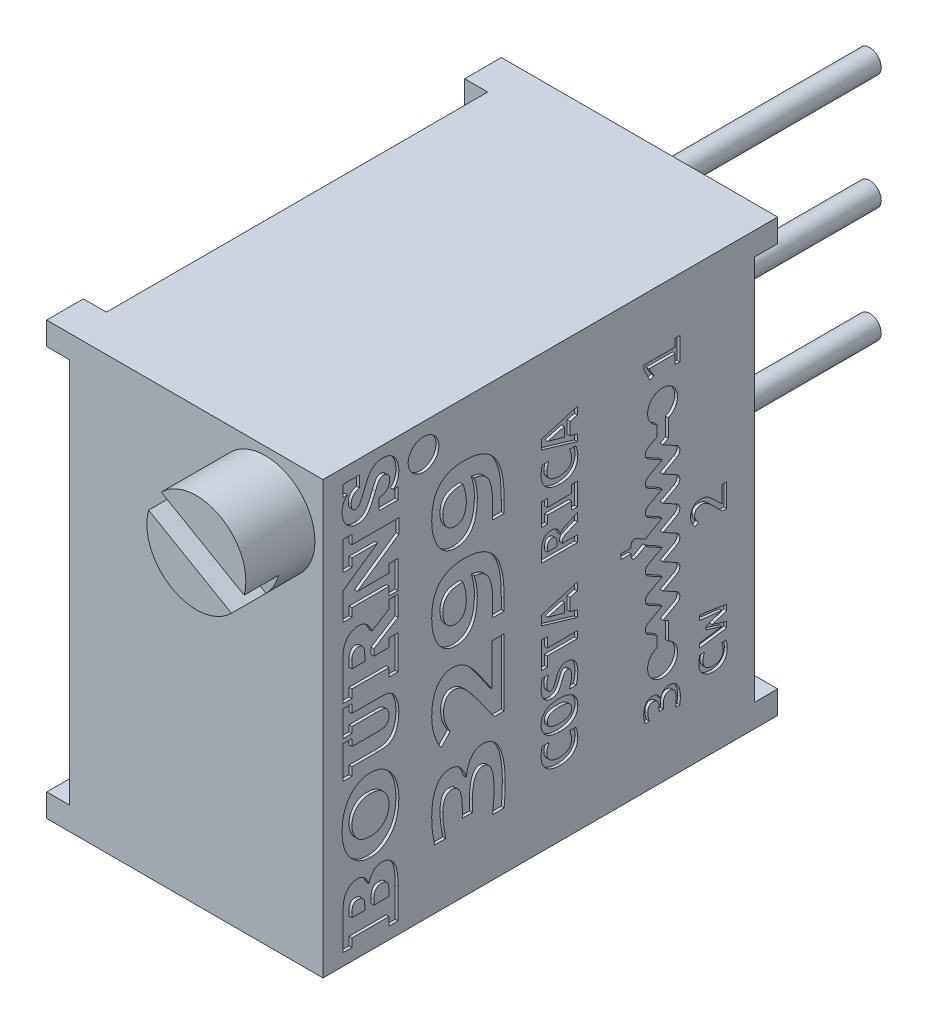
SolidWorks part; units mm, degrees
ref_plane "Front Plane" through (0, 0, 0) normal (0, 0, 1) x (1, 0, 0)
ref_plane "Top Plane" through (0, 0, 0) normal (0, 1, 0) x (1, 0, 0)
ref_plane "Right Plane" through (0, 0, 0) normal (1, 0, 0) x (0, 0, -1)
sketch "Sketch1" plane through (0, 0, 0) normal (0, 0, 1) x (1, 0, 0)
  line L0 (0, 0) -> (0, 2.2225) construction
  line L1 (-1.905, 2.2225) -> (4.191, 2.2225)
  line L2 (-1.905, 2.2225) -> (-1.905, -7.3025)
  line L3 (-1.905, -7.3025) -> (4.191, -7.3025)
  line L4 (4.191, 2.2225) -> (4.191, -7.3025)
  dimension "D1" = 1.905
  dimension "D2" = 6.096
  dimension "D3" = 9.525
  dimension "D4" = 2.2225
extrude "Boss-Extrude1" add sketch "Sketch1" along normal blind 10.033
sketch "Sketch2" plane through (4.191, 0, 0) normal (1, 0, 0) x (0, 0, -1)
  line L0 (0, -7.3025) -> (0, 2.2225) construction
  line L1 (-0.508, 1.7145) -> (0, 1.7145)
  line L2 (-0.508, 1.7145) -> (-0.508, -6.7945)
  line L3 (-0.508, -6.7945) -> (0, -6.7945)
  line L4 (0, 1.7145) -> (0, -6.7945)
  line L5 (-10.033, -7.3025) -> (0, -7.3025) construction
  line L6 (-10.033, 2.2225) -> (0, 2.2225) construction
  dimension "D1" = 0.508
  dimension "D2" = 0.508
  dimension "D3" = 0.508
extrude "Cut-Extrude1" cut sketch "Sketch2" against normal through all
sketch "Sketch3" plane through (0, 0, 0.508) normal (0, 0, -1) x (-1, 0, 0)
  line L0 (-1.143, 2.2225) -> (-1.143, -7.3025) construction
  line L1 (-4.191, 2.2225) -> (1.905, 2.2225) construction
  line L2 (1.905, -7.3025) -> (-4.191, -7.3025) construction
  circle A0 centre (0, 0) radius 0.254
  circle A1 centre (0, -2.54) radius 0.254
  circle A2 centre (0, -5.08) radius 0.254
  dimension "D1" = 0.508
  dimension "D4" = 1.143
  dimension "D3" = 2.54
  dimension "D2" = 3
extrude "Boss-Extrude2" add sketch "Sketch3" along normal blind 6.731
sketch "Sketch4" plane through (-1.905, 0, 0) normal (-1, 0, 0) x (0, 0, 1)
  line L0 (0.508, -6.7945) -> (0.508, 1.7145)
  line L1 (10.033, 2.2225) -> (0, 2.2225) construction
  line L2 (10.033, -7.3025) -> (0, -7.3025) construction
  line L3 (9.2227, 2.2225) -> (9.2227, 1.7145)
  line L4 (0.508, 1.7145) -> (0.508, -6.7945) construction
  line L5 (10.033, 2.2225) -> (10.033, -7.3025) construction
  line L6 (9.2227, 1.7145) -> (10.033, 1.7145)
  line L7 (9.2227, -6.7945) -> (10.033, -6.7945)
  line L8 (0.8103, 2.2225) -> (9.2227, 2.2225)
  line L9 (10.033, 1.7145) -> (10.033, -6.7945)
  line L10 (0.8103, -7.3025) -> (9.2227, -7.3025)
  line L11 (9.2227, -6.7945) -> (9.2227, -7.3025)
  line L12 (0.8103, 2.2225) -> (0.8103, 1.7145)
  line L13 (0.8103, 1.7145) -> (0.508, 1.7145)
  line L14 (0, 2.2225) -> (0, 1.7145) construction
  line L15 (0.8103, -7.3025) -> (0.8103, -6.7945)
  line L16 (0.8103, -6.7945) -> (0.508, -6.7945)
  dimension "D1" = 0.8103
  dimension "D2" = 0.508
  dimension "D3" = 0.508
  dimension "D4" = 0.8103
extrude "Cut-Extrude3" cut sketch "Sketch4" against normal blind 0.508
sketch "Sketch5" plane through (0, 0, 10.033) normal (0, 0, 1) x (1, 0, 0)
  line L0 (4.191, 2.2225) -> (-1.905, 2.2225) construction
  line L1 (4.191, -7.3025) -> (4.191, 2.2225) construction
  circle A0 centre (2.921, 0.9525) radius 1.0922
  dimension "D3" = 2.1844
  dimension "D1" = 1.27
  dimension "D2" = 1.27
extrude "Boss-Extrude3" add sketch "Sketch5" along normal blind 1.524
sketch "Sketch6" plane through (0, 0, 11.557) normal (0, 0, 1) x (1, 0, 0)
  line L0 (1.143, 2.2225) -> (1.143, -0.8608) construction
  line L1 (4.191, 2.2225) -> (-1.905, 2.2225) construction
  line L2 (2.1463, 1.7224) -> (3.9751, 0.6665)
  line L4 (1.8669, 1.2385) -> (3.6957, 0.1826)
  arc A0 (2.1463, 1.7224) -> (1.8669, 1.2385) centre (2.921, 0.9525) ccw
  arc A1 (3.6957, 0.1826) -> (3.9751, 0.6665) centre (2.921, 0.9525) ccw
  dimension "D3" = 1.0922
  dimension "D1" = 0.2794
  dimension "D2" = 0.5588
  dimension "D4" = 60
extrude "Cut-Extrude4" cut sketch "Sketch6" against normal blind 0.762
sketch "Sketch8" plane through (4.191, 0, 0) normal (1, 0, 0) x (0, 0, -1)
  line L0 (-2.54, -4.9784) -> (-2.54, -0.1016) construction
  line L1 (-2.54, -2.54) -> (-0.508, -2.54) construction
  line L2 (-0.508, 1.7145) -> (-0.508, -6.7945) construction
  line L3 (-2.921, -4.2164) -> (-2.159, -4.2164) construction
  line L4 (-2.921, -3.6576) -> (-2.159, -3.6576) construction
  line L5 (-2.921, -3.0988) -> (-2.159, -3.0988) construction
  line L6 (-2.54, -2.54) -> (-2.921, -2.54) construction
  line L7 (-2.921, -1.9812) -> (-2.159, -1.9812) construction
  line L8 (-2.921, -1.4224) -> (-2.159, -1.4224) construction
  line L9 (-2.921, -0.8636) -> (-2.159, -0.8636) construction
  line L10 (-2.54, -4.9784) -> (-2.921, -4.9784) construction
  line L11 (-2.54, -0.1016) -> (-2.921, -0.1016) construction
  line L12 (-2.921, -4.9784) -> (-2.921, -4.2164) construction
  line L13 (-2.921, -4.2164) -> (-2.921, -3.6576) construction
  line L14 (-2.921, -3.6576) -> (-2.921, -3.0988) construction
  line L15 (-2.921, -3.0988) -> (-2.921, -2.54) construction
  line L16 (-2.921, -2.54) -> (-2.921, -1.9812) construction
  line L17 (-2.921, -1.9812) -> (-2.921, -1.4224) construction
  line L18 (-2.921, -1.4224) -> (-2.921, -0.8636) construction
  line L19 (-2.921, -0.8636) -> (-2.921, -0.1016) construction
  line L20 (-2.667, -4.6736) -> (-2.667, -4.4312)
  line L21 (-2.667, -4.4312) -> (-2.8552, -4.3277)
  line L22 (-2.159, -4.2164) -> (-2.159, -0.8636) construction
  line L23 (-2.8552, -4.1051) -> (-2.5495, -3.937)
  line L24 (-2.413, -4.6736) -> (-2.413, -4.281)
  line L25 (-2.413, -4.281) -> (-2.5305, -4.2164)
  line L26 (-2.5305, -4.2164) -> (-2.2248, -4.0483)
  line L27 (-2.667, -4.6736) -> (-2.54, -4.6736) construction
  line L28 (-2.54, -4.6736) -> (-2.413, -4.6736) construction
  line L29 (-2.5495, -3.937) -> (-2.8552, -3.7689)
  line L30 (-2.8552, -3.5463) -> (-2.5495, -3.3782)
  line L31 (-2.5305, -3.6576) -> (-2.2248, -3.8257)
  line L32 (-2.921, -3.937) -> (-2.159, -3.937) construction
  line L33 (-2.5305, -3.6576) -> (-2.2248, -3.4895)
  line L34 (-2.7611, -4.3794) -> (-2.6387, -4.1569) construction
  line L35 (-2.667, -4.4312) -> (-2.413, -4.4312) construction
  line L36 (-2.921, -3.3782) -> (-2.159, -3.3782) construction
  line L37 (-2.921, -2.8194) -> (-2.159, -2.8194) construction
  line L38 (-2.5495, -3.3782) -> (-2.8552, -3.2101)
  line L39 (-2.8552, -2.9875) -> (-2.5495, -2.8194)
  line L40 (-2.921, -2.2606) -> (-2.159, -2.2606) construction
  line L41 (-2.921, -1.7018) -> (-2.159, -1.7018) construction
  line L42 (-2.921, -1.143) -> (-2.159, -1.143) construction
  line L43 (-2.5495, -2.8194) -> (-2.8552, -2.6513)
  line L44 (-2.8552, -2.4287) -> (-2.5495, -2.2606)
  line L45 (-2.5495, -2.2606) -> (-2.8552, -2.0925)
  line L46 (-2.8552, -1.8699) -> (-2.5495, -1.7018)
  line L47 (-2.5495, -1.7018) -> (-2.8552, -1.5337)
  line L48 (-2.8552, -1.3111) -> (-2.5495, -1.143)
  line L49 (-2.5495, -1.143) -> (-2.8552, -0.9749)
  line L50 (-2.8552, -0.7523) -> (-2.667, -0.6488)
  line L51 (-2.667, -0.6488) -> (-2.667, -0.4064)
  line L52 (-2.2248, -3.2669) -> (-2.5305, -3.0988)
  line L53 (-2.5305, -3.0988) -> (-2.2248, -2.9307)
  line L54 (-2.2248, -2.7081) -> (-2.5305, -2.54)
  line L55 (-2.5305, -2.54) -> (-2.2248, -2.3719)
  line L56 (-2.2248, -2.1493) -> (-2.5305, -1.9812)
  line L57 (-2.5305, -1.9812) -> (-2.2248, -1.8131)
  line L58 (-2.2248, -1.5905) -> (-2.5305, -1.4224)
  line L59 (-2.5305, -1.4224) -> (-2.2248, -1.2543)
  line L60 (-2.2248, -1.0317) -> (-2.5305, -0.8636)
  line L61 (-2.5305, -0.8636) -> (-2.413, -0.799)
  line L62 (-2.413, -0.799) -> (-2.413, -0.4064)
  line L63 (-8.3765, -7.3025) -> (-8.3765, 2.2225) construction
  line L64 (-10.033, -7.3025) -> (0, -7.3025) construction
  line L65 (-6.0359, -7.3025) -> (-6.0359, 2.2225) construction
  line L66 (-10.033, 2.2225) -> (0, 2.2225) construction
  line L67 (-2.159, -6.431) -> (-2.159, -5.1421) construction
  line L68 (-2.921, -2.54) -> (-4.274, -2.54) construction
  line L69 (-2.8552, -2.6513) -> (-3.4588, -2.6513) construction
  line L70 (-2.8552, -2.4287) -> (-3.4588, -2.4287) construction
  line L71 (-3.157, -2.6513) -> (-3.157, -2.4287) construction
  line L72 (-3.4588, -2.6513) -> (-3.4588, -2.54) construction
  line L73 (-3.4588, -2.4287) -> (-3.4588, -2.54) construction
  line L74 (-3.4588, -2.5956) -> (-3.2332, -2.5956) construction
  line L75 (-3.4588, -2.4844) -> (-3.2332, -2.4844) construction
  line L76 (-3.1201, -2.362) -> (-2.9189, -2.4733)
  line L77 (-3.1201, -2.718) -> (-2.9189, -2.6067)
  line L78 (-3.2332, -2.6513) -> (-3.2332, -2.5956)
  line L79 (-3.4588, -2.5956) -> (-3.2332, -2.5956)
  line L80 (-3.4588, -2.5956) -> (-3.4588, -2.4844)
  line L81 (-3.4588, -2.4844) -> (-3.2332, -2.4844)
  line L82 (-3.2232, -2.5956) -> (-3.157, -2.5956) construction
  line L83 (-3.2278, -2.4844) -> (-3.157, -2.4844) construction
  line L84 (-3.2332, -2.4844) -> (-3.2332, -2.4287)
  line L85 (-2.159, 0.2344) -> (-2.159, 1.3077) construction
  line L86 (-1.1253, -3.0988) -> (-1.1253, -1.9812) construction
  line L87 (-1.1253, -5.9727) -> (-1.1253, -4.3794) construction
  line L88 (-4.4222, -7.3025) -> (-4.4222, 2.2225) construction
  line L89 (-10.033, -7.3025) -> (-10.033, 2.2225) construction
  arc A0 (-2.667, -4.6736) -> (-2.413, -4.6736) centre (-2.54, -4.9784) ccw
  arc A1 (-2.413, -0.4064) -> (-2.667, -0.4064) centre (-2.54, -0.1016) ccw
  arc A2 (-2.8552, -4.3277) -> (-2.8552, -4.1051) centre (-2.794, -4.2164) cw
  arc A3 (-2.8552, -3.7689) -> (-2.8552, -3.5463) centre (-2.794, -3.6576) cw
  arc A4 (-2.2248, -4.0483) -> (-2.2248, -3.8257) centre (-2.286, -3.937) ccw
  arc A5 (-2.8552, -3.2101) -> (-2.8552, -2.9875) centre (-2.794, -3.0988) cw
  arc A6 (-2.8552, -2.6513) -> (-2.9068, -2.5983) centre (-2.794, -2.54) cw
  arc A7 (-2.8552, -2.0925) -> (-2.8552, -1.8699) centre (-2.794, -1.9812) cw
  arc A8 (-2.8552, -1.5337) -> (-2.8552, -1.3111) centre (-2.794, -1.4224) cw
  arc A9 (-2.8552, -0.9749) -> (-2.8552, -0.7523) centre (-2.794, -0.8636) cw
  arc A10 (-2.2248, -3.4895) -> (-2.2248, -3.2669) centre (-2.286, -3.3782) ccw
  arc A11 (-2.2248, -2.9307) -> (-2.2248, -2.7081) centre (-2.286, -2.8194) ccw
  arc A12 (-2.2248, -2.3719) -> (-2.2248, -2.1493) centre (-2.286, -2.2606) ccw
  arc A13 (-2.2248, -1.8131) -> (-2.2248, -1.5905) centre (-2.286, -1.7018) ccw
  arc A14 (-2.2248, -1.2543) -> (-2.2248, -1.0317) centre (-2.286, -1.143) ccw
  circle A15 centre (-7.8146, 1.5938) radius 0.3388
  arc A16 (-2.9189, -2.6067) -> (-2.9068, -2.5983) centre (-2.9558, -2.54) ccw
  arc A17 (-3.1201, -2.362) -> (-3.2332, -2.4287) centre (-3.157, -2.4287) ccw
  arc A18 (-3.2332, -2.6513) -> (-3.1201, -2.718) centre (-3.157, -2.6513) ccw
  arc A19 (-2.9068, -2.4817) -> (-2.8552, -2.4287) centre (-2.794, -2.54) cw
  arc A20 (-2.9068, -2.4817) -> (-2.9189, -2.4733) centre (-2.9558, -2.54) ccw
  text T0 "BOURNS" font "Rockwell" height in points 5
  text T1 "3299" font "Consolas" height in points 6
  text T2 "3" font "Consolas" height in points 3
  text T3 "1" font "Consolas" height in points 3
  text T4 "2" font "Consolas" height in points 3
  text T5 "cw" font "Consolas" height in points 3
  text T6 "COSTA RICA" font "Consolas" height in points 3
  point P20 (-2.54, -0.8636)
  dimension "D1" = 0.6604
  dimension "D2" = 0.5588
  dimension "D9" = 0.127
  dimension "D7" = 0.1524
  dimension "D10" = 0.1524
  dimension "D11" = 0.1524
  dimension "D3" = 0.762
  dimension "D4" = 2.032
  dimension "D5" = 0.381
  dimension "D6" = 0.1618
  dimension "D8" = 0.127
  dimension "D12" = 0.2012
  dimension "D13" = 1.651
  dimension "D14" = 0.6173
  dimension "D15" = 1.6565
  dimension "D16" = 3.9971
  dimension "D17" = 5.6108
extrude "Cut-Extrude5" cut sketch "Sketch8" against normal blind 0.0635
equation "\"0.012n\"=0.0118821"
